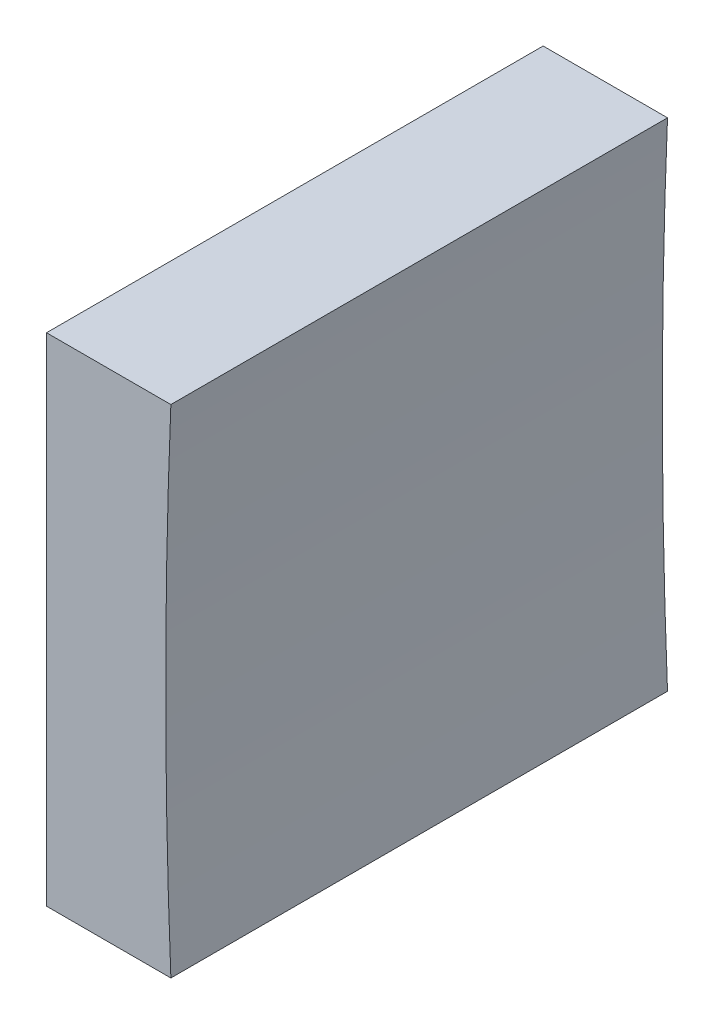
SolidWorks part; units mm, degrees
ref_plane "前视基准面" through (0, 0, 0) normal (0, 0, 1) x (1, 0, 0)
ref_plane "上视基准面" through (0, 0, 0) normal (0, 1, 0) x (1, 0, 0)
ref_plane "右视基准面" through (0, 0, 0) normal (1, 0, 0) x (0, 0, -1)
sketch "草图1" plane through (0, 0, 0) normal (0, 0, 1) x (1, 0, 0)
  line L0 (139.3275, 33.429) -> (149.0915, 33.429) construction
  line L1 (142.3536, 33.429) -> (142.3536, 39.679)
  line L2 (142.3536, 39.679) -> (145.4838, 39.679)
  line L3 (145.4838, 27.179) -> (142.3536, 27.179)
  line L4 (142.3536, 27.179) -> (142.3536, 33.429)
  arc A0 (145.4838, 39.679) -> (145.4838, 27.179) centre (295.3536, 33.429) ccw
  dimension "D1" = 150
  dimension "D2" = 3.1303
extrude "凸台-拉伸1" add sketch "草图1" along normal blind 12.5
